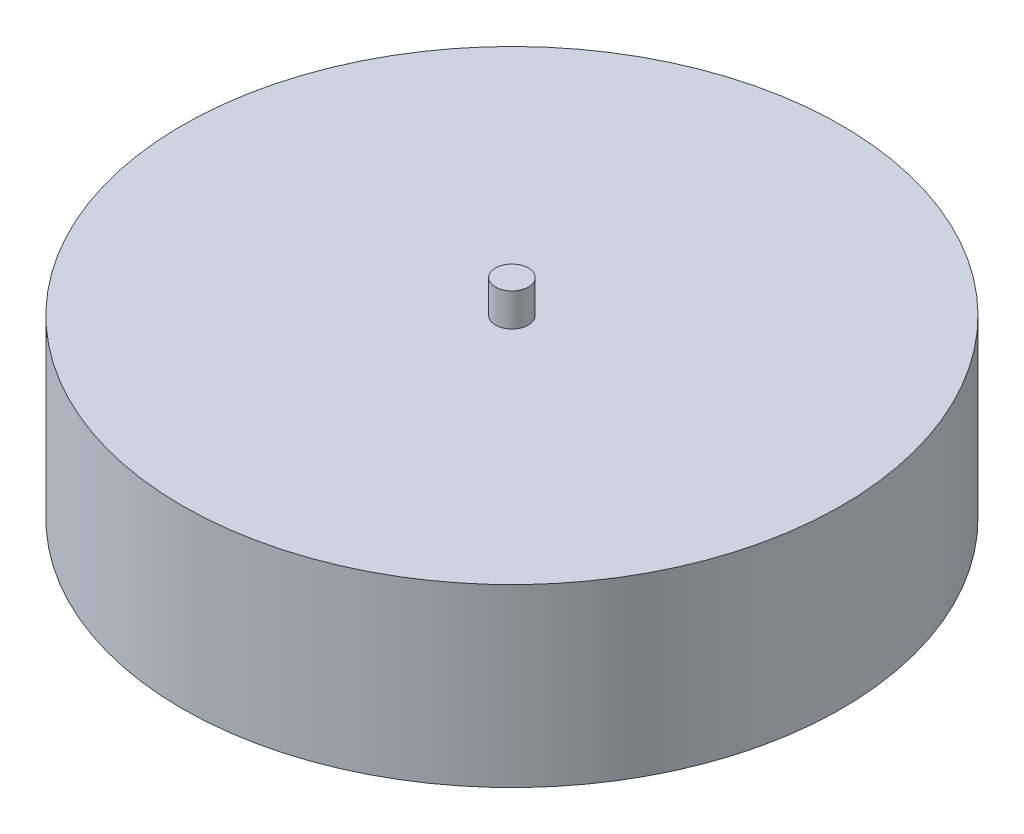
SolidWorks part; units mm, degrees
ref_plane "Front Plane" through (0, 0, 0) normal (0, 0, 1) x (1, 0, 0)
ref_plane "Top Plane" through (0, 0, 0) normal (0, 1, 0) x (1, 0, 0)
ref_plane "Right Plane" through (0, 0, 0) normal (1, 0, 0) x (0, 0, -1)
sketch "Sketch1" plane through (0, 0, 0) normal (0, 1, 0) x (1, 0, 0)
  circle A0 centre (0, 0) radius 60
  dimension "D1" = 120
extrude "Boss-Extrude1" add sketch "Sketch1" along normal blind 32
sketch "Sketch2" plane through (0, 32, 0) normal (0, 1, 0) x (1, 0, 0)
  circle A0 centre (0, 0) radius 3
  dimension "D1" = 6
extrude "Boss-Extrude2" add sketch "Sketch2" along normal blind 6
